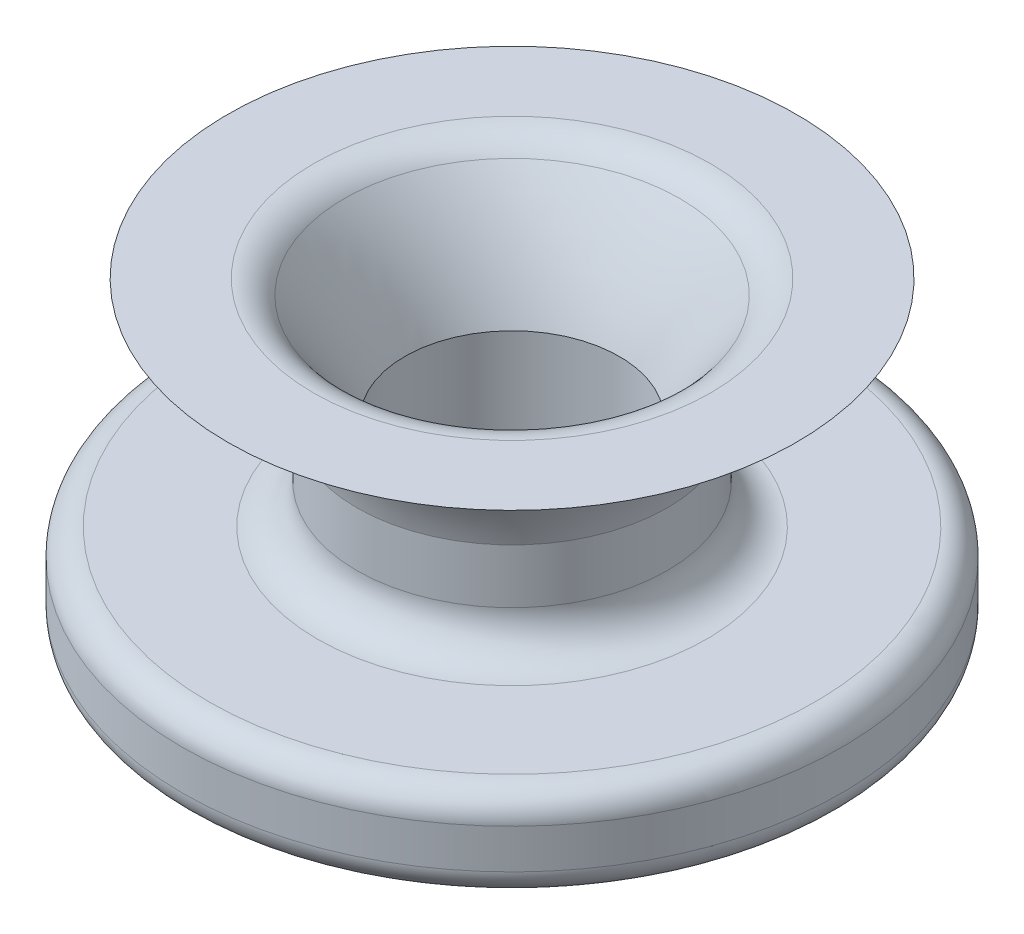
SolidWorks part; units mm, degrees
ref_plane "Front Plane" through (0, 0, 0) normal (0, 0, 1) x (1, 0, 0)
ref_plane "Top Plane" through (0, 0, 0) normal (0, 1, 0) x (1, 0, 0)
ref_plane "Right Plane" through (0, 0, 0) normal (1, 0, 0) x (0, 0, -1)
sketch "Sketch1" plane through (0, 0, 0) normal (0, 1, 0) x (1, 0, 0)
  line L5 (-44.9013, 44.9013) -> (44.9013, -44.9013) construction
  line L6 (-44.9013, -44.9013) -> (44.9013, 44.9013) construction
  circle A0 centre (0, 0) radius 63.5
  point P0 (0, 0)
extrude "Boss-Extrude1" add sketch "Sketch1" along normal blind 17.78
sketch "Sketch4" plane through (0, 0, 0) normal (0, -1, 0) x (1, 0, 0)
  circle A0 centre (0, 0) radius 25.3666
extrude "Boss-Extrude6" add sketch "Sketch4" along normal blind 20.32
sketch "Sketch6" plane through (0, -20.32, 0) normal (0, -1, 0) x (1, 0, 0)
  circle A0 centre (0, 0) radius 19.05
  dimension "D1" = 38.1
extrude "Cut-Extrude1" cut sketch "Sketch6" against normal blind 20.32
ref_plane "Plane1" through (0, 0, -25.3666) normal (0, 0, -1) x (-1, 0, 0)
sketch "Sketch12" plane through (0, 0, -25.3666) normal (0, 0, -1) x (-1, 0, 0)
  circle A0 centre (0, -10.2489) radius 3.81
  dimension "D1" = 7.62
extrude "Cut-Extrude6" cut sketch "Sketch12" against normal through all both
fillet "Fillet2" radius 5.08 2 edges at (0, 0, -25.3666) (0, 0, 63.5)
fillet "Fillet4" radius 2.54 1 edges at (0, -20.32, -19.05)
fillet "Fillet5" radius 5.08 1 edges at (0, 17.78, 63.5)
sketch "Sketch15" plane through (0, 0, 0) normal (0, 0, 1) x (1, 0, 0)
  line L0 (-29.892, 17.78) -> (-29.892, 35.8641)
  line L1 (58.42, 17.78) -> (-58.42, 17.78) construction
  line L2 (-54.7651, 59.2336) -> (0, 59.2336)
  line L3 (0, 59.2336) -> (0, 17.78)
  line L4 (0, 17.78) -> (-29.892, 17.78)
  spline S0 degree 2 poles (-29.892, 35.8641) (-34.4697, 58.1776) (-54.7651, 59.2336) knots 0 0 0 1 1 1
revolve "Revolve2" add sketch "Sketch15" angle 360 about L3
sketch "Sketch17" plane through (0, 0, 0) normal (0, 0, 1) x (1, 0, 0)
  line L0 (-20.6738, 17.7891) -> (-20.6738, 35.8641)
  line L1 (29.892, 35.8641) -> (-29.892, 35.8641) construction
  line L2 (-36.4603, 61.1065) -> (0, 61.1065)
  line L3 (0, 61.1065) -> (0, 17.7891)
  line L4 (0, 17.7891) -> (-20.6738, 17.7891)
  spline S0 degree 2 poles (-20.6738, 35.8641) (-26.0333, 50.1709) (-36.4603, 61.1065) knots 0 0 0 1 1 1
revolve "Cut-Revolve2" cut sketch "Sketch17" angle 360 about L3
fillet "Fillet6" radius 7.62 1 edges at (0, 17.78, 29.892)
fillet "Fillet7" radius 7.62 1 edges at (0, 59.2336, 34.7338)
